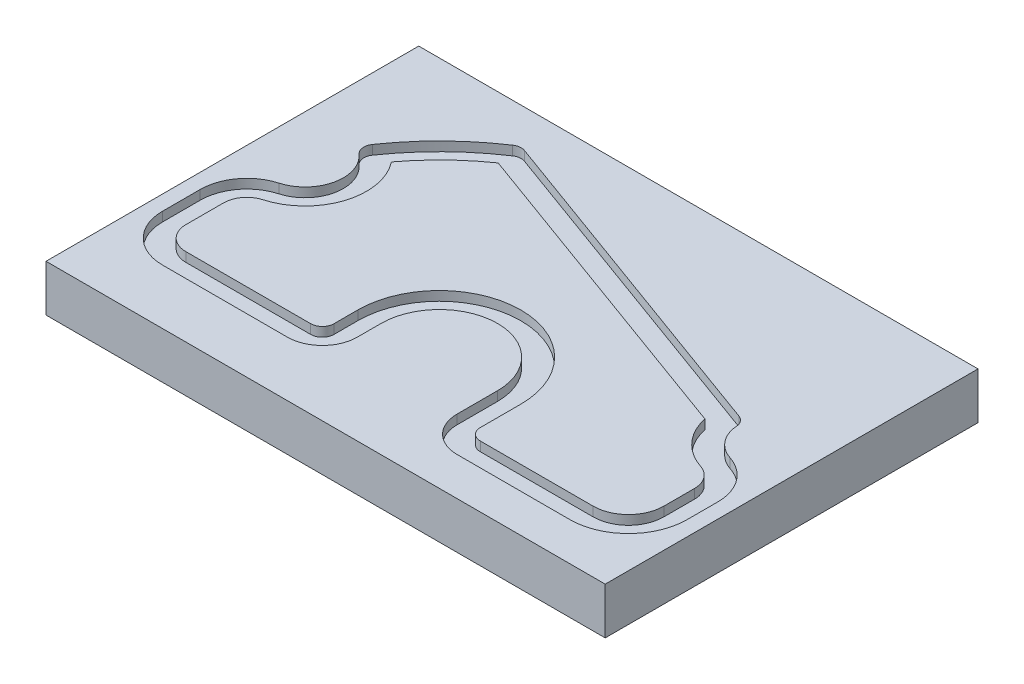
SolidWorks part; units mm, degrees
ref_plane "Front Plane" through (0, 0, 0) normal (0, 0, 1) x (1, 0, 0)
ref_plane "Top Plane" through (0, 0, 0) normal (0, 1, 0) x (1, 0, 0)
ref_plane "Right Plane" through (0, 0, 0) normal (1, 0, 0) x (0, 0, -1)
sketch "Sketch1" plane through (0, 0, 0) normal (0, 1, 0) x (1, 0, 0)
  line L0 (-59.436, -9.652) -> (-25.4, -9.652)
  line L1 (-22.225, -6.477) -> (-22.225, 0)
  line L2 (22.225, 0) -> (22.225, -11.049)
  line L3 (25.4, -14.224) -> (56.134, -14.224)
  line L4 (65.786, -4.572) -> (65.786, 3.7863)
  line L5 (-37.8039, 53.8392) -> (50.8, 21.59)
  line L6 (-65.786, -3.302) -> (-65.786, 6.9854)
  arc A0 (-22.225, 0) -> (22.225, 0) centre (0, 0) cw
  arc A1 (50.8, 21.59) -> (61.3983, 9.8255) centre (66.294, 24.892) ccw
  arc A2 (-61.1805, 13.091) -> (-52.5801, 39.5365) centre (-65.786, 29.21) ccw
  arc A3 (-37.8039, 53.8392) -> (-52.5801, 39.5365) centre (0, 0) ccw
  arc A4 (22.225, -11.049) -> (25.4, -14.224) centre (25.4, -11.049) ccw
  arc A5 (-25.4, -9.652) -> (-22.225, -6.477) centre (-25.4, -6.477) ccw
  arc A6 (56.134, -14.224) -> (65.786, -4.572) centre (56.134, -4.572) ccw
  arc A7 (-59.436, -9.652) -> (-65.786, -3.302) centre (-59.436, -3.302) cw
  arc A8 (-65.786, 6.9854) -> (-61.1805, 13.091) centre (-59.436, 6.9854) cw
  arc A9 (65.786, 3.7863) -> (61.3983, 9.8255) centre (59.436, 3.7863) ccw
  dimension "D1" = 3.175
  dimension "D2" = 9.652
  dimension "D3" = 6.35
extrude "Boss-Extrude1" add sketch "Sketch1" along normal blind 2.54
sketch "Sketch2" plane through (0, 0, 0) normal (0, -1, 0) x (1, 0, 0)
  line L1 (-76.2, 30.988) -> (-76.2, -70.6002)
  line L2 (76.2, 30.988) -> (76.2, -70.612)
  line L3 (-76.2, -70.6002) -> (76.2, -70.612)
  line L4 (-76.2, 30.988) -> (76.2, 30.988)
  point P0 (-76.2, 31.75)
  point P1 (-76.2, -69.85)
  point P2 (76.2, 31.75)
  point P3 (76.2, -69.85)
  point P8 (-88.9, -57.15)
  point P9 (88.9, -57.15)
  point P10 (-88.9, 19.05)
  point P11 (88.9, 19.05)
  dimension "D1" = 30.988
  dimension "D3" = 16.764
  dimension "6." = 152.4
extrude "Boss-Extrude2" add sketch "Sketch2" along normal blind 10.16
sketch "Sketch9" plane through (0, 2.54, 0) normal (0, 1, 0) x (1, 0, 0)
  line L97 (76.2, -30.988) -> (76.2, 70.612)
  line L98 (15.875, 0) -> (15.875, -11.049)
  line L99 (25.4, -20.574) -> (56.134, -20.574)
  line L100 (72.136, -4.572) -> (72.136, 3.7863)
  line L101 (56.8835, 26.1333) -> (-38.6533, 60.9059)
  line L102 (-72.136, 6.9854) -> (-72.136, -3.302)
  line L103 (-59.436, -16.002) -> (-25.4, -16.002)
  line L104 (-15.875, -6.477) -> (-15.875, 0)
  line L105 (15.875, 0) -> (15.875, -11.049)
  line L106 (25.4, -20.574) -> (56.134, -20.574)
  line L107 (72.136, -4.572) -> (72.136, 3.7863)
  line L108 (56.8835, 26.1333) -> (-38.6533, 60.9059)
  line L109 (-72.136, 6.9854) -> (-72.136, -3.302)
  line L110 (-59.436, -16.002) -> (-25.4, -16.002)
  line L111 (-15.875, -6.477) -> (-15.875, 0)
  line L112 (-76.2, -30.988) -> (76.2, -30.988)
  line L113 (-76.2, 70.6002) -> (-76.2, -30.988)
  line L114 (76.2, 70.612) -> (-76.2, 70.6002)
  line L115 (76.2, -30.988) -> (76.2, 70.612)
  line L116 (-76.2, -30.988) -> (76.2, -30.988)
  line L117 (-76.2, 70.6002) -> (-76.2, -30.988)
  line L118 (76.2, 70.612) -> (-76.2, 70.6002)
  arc A33 (15.875, 0) -> (-15.875, 0) centre (0, 0) ccw
  arc A34 (15.875, 0) -> (-15.875, 0) centre (0, 0) ccw
  arc A138 (15.875, 0) -> (-15.875, 0) centre (0, 0) ccw
  arc A139 (15.875, -11.049) -> (25.4, -20.574) centre (25.4, -11.049) ccw
  arc A140 (56.134, -20.574) -> (72.136, -4.572) centre (56.134, -4.572) ccw
  arc A141 (72.136, 3.7863) -> (63.3607, 15.8646) centre (59.436, 3.7863) ccw
  arc A142 (56.8835, 26.1333) -> (63.3607, 15.8646) centre (66.294, 24.892) ccw
  arc A143 (-38.6533, 60.9059) -> (-61.0217, 38.4703) centre (0, 0) ccw
  arc A144 (-62.925, 19.1967) -> (-61.0217, 38.4703) centre (-65.786, 29.21) ccw
  arc A145 (-62.925, 19.1967) -> (-72.136, 6.9854) centre (-59.436, 6.9854) ccw
  arc A146 (-72.136, -3.302) -> (-59.436, -16.002) centre (-59.436, -3.302) ccw
  arc A147 (-25.4, -16.002) -> (-15.875, -6.477) centre (-25.4, -6.477) ccw
  arc A149 (15.875, -11.049) -> (25.4, -20.574) centre (25.4, -11.049) ccw
  arc A150 (56.134, -20.574) -> (72.136, -4.572) centre (56.134, -4.572) ccw
  arc A151 (72.136, 3.7863) -> (63.3607, 15.8646) centre (59.436, 3.7863) ccw
  arc A152 (56.8835, 26.1333) -> (63.3607, 15.8646) centre (66.294, 24.892) ccw
  arc A153 (-38.6533, 60.9059) -> (-61.0217, 38.4703) centre (0, 0) ccw
  arc A154 (-62.925, 19.1967) -> (-61.0217, 38.4703) centre (-65.786, 29.21) ccw
  arc A155 (-62.925, 19.1967) -> (-72.136, 6.9854) centre (-59.436, 6.9854) ccw
  arc A156 (-72.136, -3.302) -> (-59.436, -16.002) centre (-59.436, -3.302) ccw
  arc A157 (-25.4, -16.002) -> (-15.875, -6.477) centre (-25.4, -6.477) ccw
  dimension "D1" = 6.35
  dimension "D2" = 0
  dimension "D3" = 6.35
extrude "Boss-Extrude4" add sketch "Sketch9" against normal blind 2.54
fillet "Fillet1" radius 3.175 1 edges at (-38.6533, 1.27, -60.9059)
fillet "Fillet2" radius 3.175 1 edges at (56.8835, 1.27, -26.1333)
fillet "Fillet3" radius 3.175 1 edges at (-61.0217, 1.27, -38.4703)
